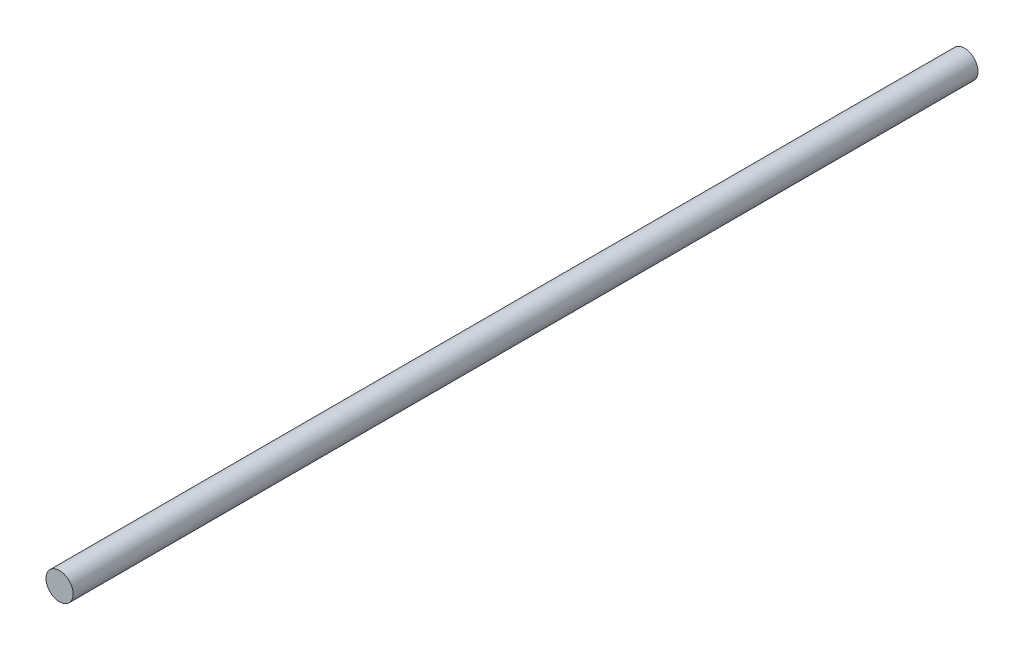
SolidWorks part; units mm, degrees
material "Plain Carbon Steel"
ref_plane "Front Plane" through (0, 0, 0) normal (0, 0, 1) x (1, 0, 0)
ref_plane "Top Plane" through (0, 0, 0) normal (0, 1, 0) x (1, 0, 0)
ref_plane "Right Plane" through (0, 0, 0) normal (1, 0, 0) x (0, 0, -1)
sketch "Sketch1" plane through (0, 0, 0) normal (0, 0, 1) x (1, 0, 0)
  circle A0 centre (0, 0) radius 1.5
  dimension "D1" = 3
extrude "Boss-Extrude1" add sketch "Sketch1" along normal blind 100
